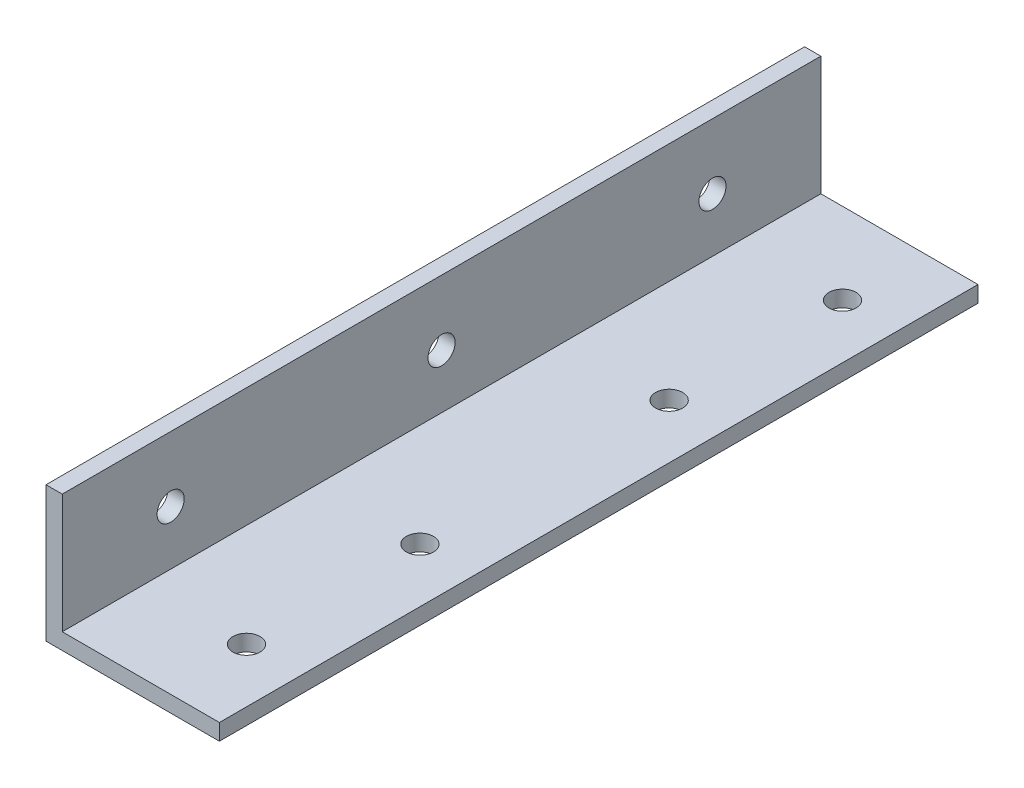
SolidWorks part; units mm, degrees
ref_plane "Front Plane" through (0, 0, 0) normal (0, 0, 1) x (1, 0, 0)
ref_plane "Top Plane" through (0, 0, 0) normal (0, 1, 0) x (1, 0, 0)
ref_plane "Right Plane" through (0, 0, 0) normal (1, 0, 0) x (0, 0, -1)
sketch "Sketch2" plane through (0, 0, 0) normal (0, 0, 1) x (1, 0, 0)
  line L0 (-10.0379, 20.4483) -> (-10.0379, -1.5517)
  line L1 (-10.0379, -1.5517) -> (18.9621, -1.5517)
  line L2 (18.9621, -1.5517) -> (18.9621, -4.5517)
  line L3 (18.9621, -4.5517) -> (-13.0379, -4.5517)
  line L4 (-13.0379, -4.5517) -> (-13.0379, 20.4483)
  line L5 (-13.0379, 20.4483) -> (-10.0379, 20.4483)
  dimension "D1" = 25
  dimension "D2" = 32
  dimension "D3" = 3
  dimension "D4" = 3
extrude "Boss-Extrude2" add sketch "Sketch2" along normal blind 140
hole_wizard "Hole for M5 300® SC Nuts (SP)1" positions "3DSketch1" profile "Sketch3" hole size "M5x0.8" standard "PEM® Metric" end condition through all
sketch3d "3DSketch1"
  line L0 (18.9621, -1.5517, 140) -> (18.9621, -1.5517, 0) construction
  line L1 (18.9621, -1.5517, 0) -> (-10.0379, -1.5517, 0) construction
  line L2 (18.9621, -1.5517, 140) -> (-10.0379, -1.5517, 140) construction
  point P0 (8.9621, -1.5517, 15)
  point P2 (8.9621, -1.5517, 47)
  point P4 (8.9621, -1.5517, 93)
  point P6 (8.9621, -1.5517, 125)
  dimension "D1" = 10
  dimension "D2" = 15
  dimension "D3" = 32
  dimension "D4" = 15
  dimension "D5" = 32
sketch "Sketch3" plane through (8.9621, -1.5517, 15) normal (1, 0, 0) x (0, 0, 1)
  line L0 (0, 0) -> (0, 3)
  line L1 (0, 3) -> (2.5, 3)
  line L2 (2.5, 3) -> (2.5, 0)
  line L5 (2.5, 0) -> (0, 0)
  line L11 (0, -6.35) -> (0, 107.95) construction
  dimension "Thru Hole Dia." = 5
  dimension "Thru Hole Depth" = 3
hole_wizard "Hole for M5 300® SC Nuts (SP)2" positions "Sketch4" profile "Sketch5" hole size "M5x0.8" standard "PEM® Metric" end condition through all
sketch "Sketch4" plane through (-10.0379, 0, 0) normal (1, 0, 0) x (0, 0, -1)
  line L0 (-140, -1.5517) -> (0, -1.5517) construction
  line L1 (-140, -1.5517) -> (-140, 20.4483) construction
  line L2 (0, -1.5517) -> (0, 20.4483) construction
  point P0 (-20, 8.4483)
  point P2 (-70, 8.4483)
  point P4 (-120, 8.4483)
  point P9 (0, 0)
  point P10 (0, 0)
  point P13 (0, 0)
  point P16 (0, 0)
  point P17 (0, 0)
  dimension "D1" = 10
  dimension "D2" = 20
  dimension "D3" = 70
  dimension "D4" = 20
sketch "Sketch5" plane through (-10.0379, 8.4483, 20) normal (0, 1, 0) x (0, 0, -1)
  line L0 (0, 0) -> (0, 3)
  line L1 (0, 3) -> (2.5, 3)
  line L2 (2.5, 3) -> (2.5, 0)
  line L5 (2.5, 0) -> (0, 0)
  line L11 (0, -6.35) -> (0, 107.95) construction
  dimension "Thru Hole Dia." = 5
  dimension "Thru Hole Depth" = 3
